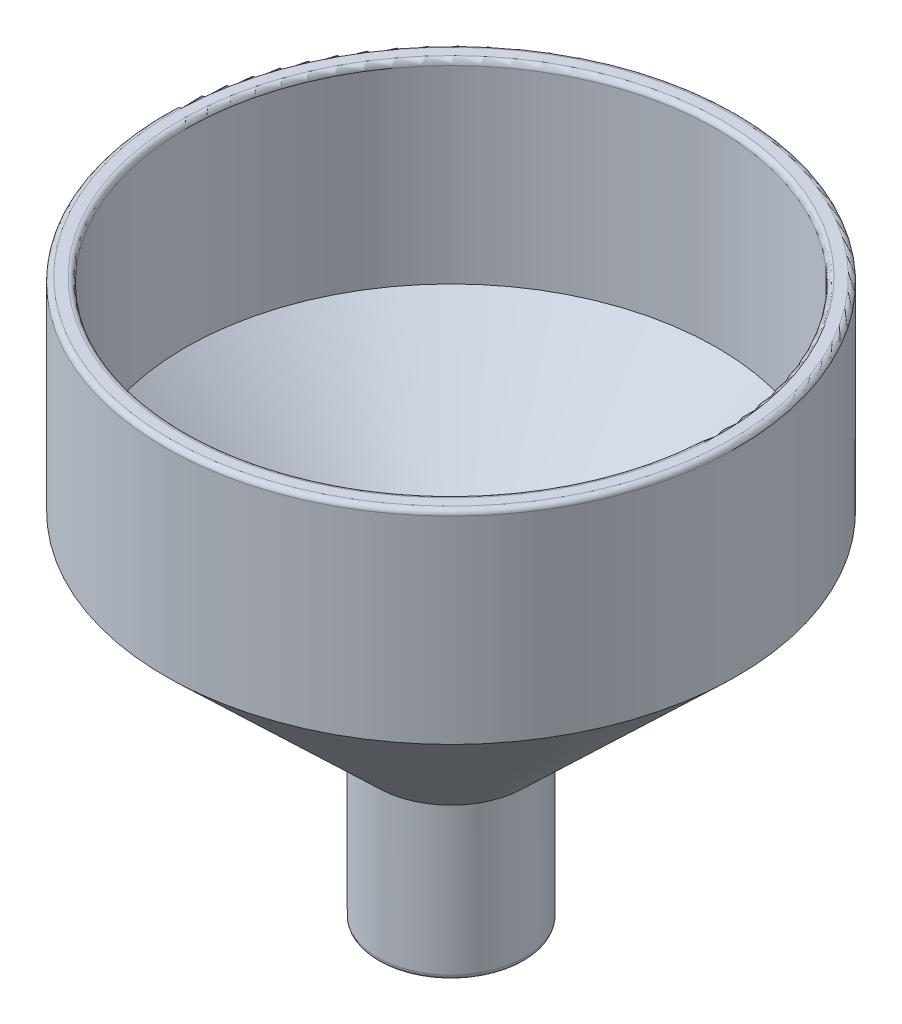
SolidWorks part; units mm, degrees
ref_plane "Front Plane" through (0, 0, 0) normal (0, 0, 1) x (1, 0, 0)
ref_plane "Top Plane" through (0, 0, 0) normal (0, 1, 0) x (1, 0, 0)
ref_plane "Right Plane" through (0, 0, 0) normal (1, 0, 0) x (0, 0, -1)
ref_axis "Axis1" through (0, 0, 0) along (0, 1, 0)
sketch "Sketch1" plane through (0, 0, 0) normal (0, 0, 1) x (1, 0, 0)
  line L0 (-5.25, 15.0833) -> (-5.25, 30.939)
  line L1 (-5.25, 30.939) -> (-26.2, 50.939)
  line L2 (-26.2, 50.939) -> (-26.2, 70.0833)
  line L3 (-26.2, 70.0833) -> (-28.2, 70.0833)
  line L4 (-28.2, 70.0833) -> (-28.2, 50.0833)
  line L5 (-28.2, 50.0833) -> (-7.25, 30.0833)
  line L6 (-7.25, 30.0833) -> (-7.25, 15.0833)
  line L7 (-7.25, 15.0833) -> (-5.25, 15.0833)
  dimension "D1" = 26.2
  dimension "D3" = 2
  dimension "D4" = 2
  dimension "wall thickness" = 2
  dimension "D6" = 15
  dimension "D7" = 20
  dimension "D8" = 20
  dimension "D2" = 7.25
revolve "Revolve1" add sketch "Sketch1" angle 360 about axis through (0, 0, 0) along (0, 1, 0)
fillet "Fillet1" radius 0.5 4 edges at (0, 70.0833, -26.2) (0, 70.0833, -28.2) (0, 15.0833, -5.25) (0, 15.0833, -7.25)
equation "\"D4@Sketch1\" = \"wall thickness\""
equation "\"D3@Sketch1\" = \"wall thickness\""
